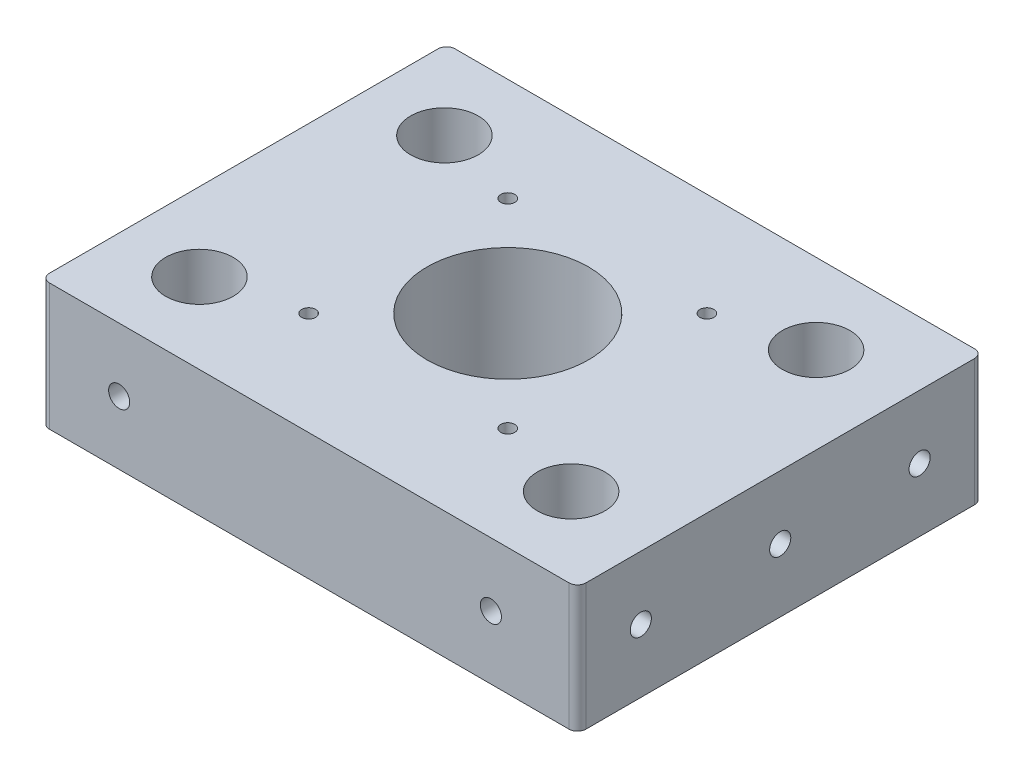
SolidWorks part; units mm, degrees
ref_plane "Front" through (0, 0, 0) normal (0, 0, 1) x (1, 0, 0)
ref_plane "Top" through (0, 0, 0) normal (0, 1, 0) x (1, 0, 0)
ref_plane "Right" through (0, 0, 0) normal (1, 0, 0) x (0, 0, -1)
sketch "Master Sketch" plane through (0, 0, 0) normal (0, 1, 0) x (1, 0, 0)
  line L1 (-62.5, -48) -> (62.5, -48) construction
  line L2 (-62.5, -48) -> (-62.5, 48) construction
  line L3 (-62.5, 48) -> (62.5, 48) construction
  line L4 (62.5, -48) -> (62.5, 48) construction
  line L5 (0, 48) -> (0, -48) construction
  line L6 (-62.5, 0) -> (62.5, 0) construction
  line L7 (-25.5, 11) -> (-62.5, 11) construction
  line L8 (-25.5, 11) -> (-25.5, 48) construction
  line L9 (-25.5, 48) -> (-62.5, 48) construction
  line L10 (-62.5, 11) -> (-62.5, 48) construction
  line L15 (25.5, 48) -> (62.5, 48) construction
  line L16 (62.5, 11) -> (62.5, 48) construction
  line L21 (25.5, -48) -> (62.5, -48) construction
  line L22 (62.5, -11) -> (62.5, -48) construction
  line L27 (-25.5, -48) -> (-62.5, -48) construction
  line L28 (-62.5, -11) -> (-62.5, -48) construction
  line L55 (-23.5712, -23.5712) -> (23.5712, -23.5712) construction
  line L56 (-23.5712, -23.5712) -> (-23.5712, 23.5712) construction
  line L57 (-23.5712, 23.5712) -> (23.5712, 23.5712) construction
  line L58 (23.5712, -23.5712) -> (23.5712, 23.5712) construction
  line L59 (0, 23.5712) -> (0, -23.5712) construction
  line L60 (-23.5712, 0) -> (23.5712, 0) construction
  circle A0 centre (0, 0) radius 12.5 construction
  circle A1 centre (44, 29) radius 8 construction
  circle A2 centre (44, -29) radius 8 construction
  circle A3 centre (-44, -29) radius 8 construction
  circle A4 centre (-44, 29) radius 8 construction
  point P0 (0, 0)
  dimension "D3" = 25
  dimension "D4" = 16
  dimension "D6" = 88
  dimension "D8" = 58
  dimension "D9" = 29
  dimension "D10" = 44
  dimension "D1" = 125
  dimension "D2" = 96
  dimension "D5" = 37
  dimension "D7" = 47.1424
sketch "Sketch2" plane through (0, 0, 0) normal (0, 1, 0) x (1, 0, 0)
  line L1 (-62.5, 48) -> (62.5, 48)
  line L2 (-62.5, 48) -> (-62.5, -48)
  line L3 (-62.5, -48) -> (62.5, -48)
  line L4 (62.5, 48) -> (62.5, -48)
  line L6 (-62.5, 0) -> (62.5, 0) construction
  circle A0 centre (-44, 29) radius 8
  circle A1 centre (-44, -29) radius 8
  circle A2 centre (44, -29) radius 8
  circle A3 centre (44, 29) radius 8
  circle A4 centre (44, 29) radius 8 construction
  circle A5 centre (-44, 29) radius 8 construction
  circle A6 centre (-44, -29) radius 8 construction
  circle A9 centre (0, 0) radius 19.1
  circle A10 centre (44, -29) radius 8 construction
  dimension "D1" = 38.2
extrude "Boss-Extrude1" add sketch "Sketch2" along normal blind 30
hole_wizard "M4x0.7 Tapped Hole1" positions "Sketch4" profile "Sketch3" tap size "M4x0.7" standard "ANSI Metric" end condition through all
sketch "Sketch4" plane through (0, 30, 0) normal (0, 1, 0) x (1, 0, 0)
  point P0 (-23.5712, 23.5712)
  point P3 (23.5712, 23.5712)
  point P6 (23.5712, -23.5712)
  point P9 (-23.5712, -23.5712)
cosmetic thread "Hole Thread1" parameters "D2"=4
cosmetic thread "Hole Thread2" parameters "D2"=4
cosmetic thread "Hole Thread3" parameters "D2"=4
cosmetic thread "Hole Thread4" parameters "D2"=4
sketch "Sketch3" plane through (-23.5712, 30, -23.5712) normal (1, 0, 0) x (0, 0, 1)
  line L0 (0, 0) -> (0, 30)
  line L1 (0, 30) -> (1.65, 30)
  line L2 (1.65, 30) -> (1.65, 0)
  line L5 (1.65, 0) -> (0, 0)
  line L11 (0, -6.35) -> (0, 107.95) construction
  dimension "Thru Tap Drill Dia." = 3.3
  dimension "Thru Tap Drill Depth" = 30
sketch "Sketch5" plane through (0, 0, 48) normal (0, 0, 1) x (1, 0, 0)
  line L4 (-62.5, 0) -> (62.5, 0)
  line L5 (62.5, 0) -> (62.5, 30)
  line L6 (62.5, 30) -> (-62.5, 30)
  line L7 (-62.5, 30) -> (-62.5, 0)
  line L8 (-62.5, 0) -> (62.5, 0)
  line L9 (62.5, 0) -> (62.5, 30)
  line L10 (62.5, 30) -> (-62.5, 30)
  line L11 (-62.5, 30) -> (-62.5, 0)
  dimension "D1" = 0
sketch "Sketch10" plane through (62.5, 0, 0) normal (1, 0, 0) x (0, 0, -1)
  line L4 (-48, 0) -> (48, 0)
  line L5 (48, 0) -> (48, 30)
  line L6 (48, 30) -> (-48, 30)
  line L7 (-48, 30) -> (-48, 0)
  line L8 (-48, 0) -> (48, 0)
  line L9 (48, 0) -> (48, 30)
  line L10 (48, 30) -> (-48, 30)
  line L11 (-48, 30) -> (-48, 0)
  dimension "D1" = 0
extrude "Boss-Extrude3" add sketch "Sketch10" along normal blind 2
hole_wizard "M6x1.0 Tapped Hole1" positions "Sketch8" profile "Sketch7" tap size "M6x1.0" standard "ANSI Metric"
sketch "Sketch8" plane through (64.5, 0, 0) normal (1, 0, 0) x (0, 0, -1)
  line L0 (-48, 15) -> (48, 15) construction
  line L3 (-48, 30) -> (-48, 0) construction
  line L4 (48, 0) -> (48, 30) construction
  line L5 (0, 30) -> (0, 0) construction
  point P0 (-33, 15)
  point P2 (0, 15)
  point P4 (33, 15)
  dimension "D1" = 33
  dimension "D2" = 33
sketch "Sketch7" plane through (64.5, 15, 33) normal (0, 1, 0) x (0, 0, -1)
  line L0 (0, 0) -> (0, 12.5022)
  line L1 (0, 12.5022) -> (2.5, 11)
  line L2 (2.5, 11) -> (2.5, 0)
  line L5 (2.5, 0) -> (0, 0)
  line L10 (0, 12.5022) -> (-2.5, 11) construction
  line L11 (0, -6.35) -> (0, 107.95) construction
  dimension "Tap Drill Dia." = 5
  dimension "Tap Drill Depth" = 11
  dimension "Drill Angle" = 118
cosmetic thread "Hole Thread6" parameters "D1"=8, "D2"=6
cosmetic thread "Hole Thread7" parameters "D1"=8, "D2"=6
cosmetic thread "Hole Thread8" parameters "D1"=8, "D2"=6
hole_wizard "M6x1.0 Tapped Hole3" positions "Sketch14" profile "Sketch13" tap size "M6x1.0" standard "ANSI Metric"
sketch "Sketch14" plane through (0, 0, -48) normal (0, 0, -1) x (-1, 0, 0)
  line L0 (44, 30) -> (44, 0) construction
  line L1 (-44, 30) -> (-44, 0) construction
  point P0 (-44, 15)
  point P2 (44, 15)
sketch "Sketch13" plane through (44, 15, -48) normal (1, 0, 0) x (0, 1, 0)
  line L0 (0, 0) -> (0, 69)
  line L1 (0, 69) -> (2.5, 69)
  line L2 (2.5, 69) -> (2.5, 0)
  line L5 (2.5, 0) -> (0, 0)
  line L11 (0, -6.35) -> (0, 107.95) construction
  dimension "Thru Tap Drill Dia." = 5
  dimension "Thru Tap Drill Depth" = 69
cosmetic thread "Hole Thread11" parameters "D2"=6
cosmetic thread "Hole Thread12" parameters "D2"=6
fillet "Fillet1" radius 2 4 edges at (-62.5, 15, -48) (64.5, 15, -48) (64.5, 15, 48) (-62.5, 15, 48)
mirror "Mirror1" about plane through (0, 0, 0) normal (0, 0, 1) of "M6x1.0 Tapped Hole3"
